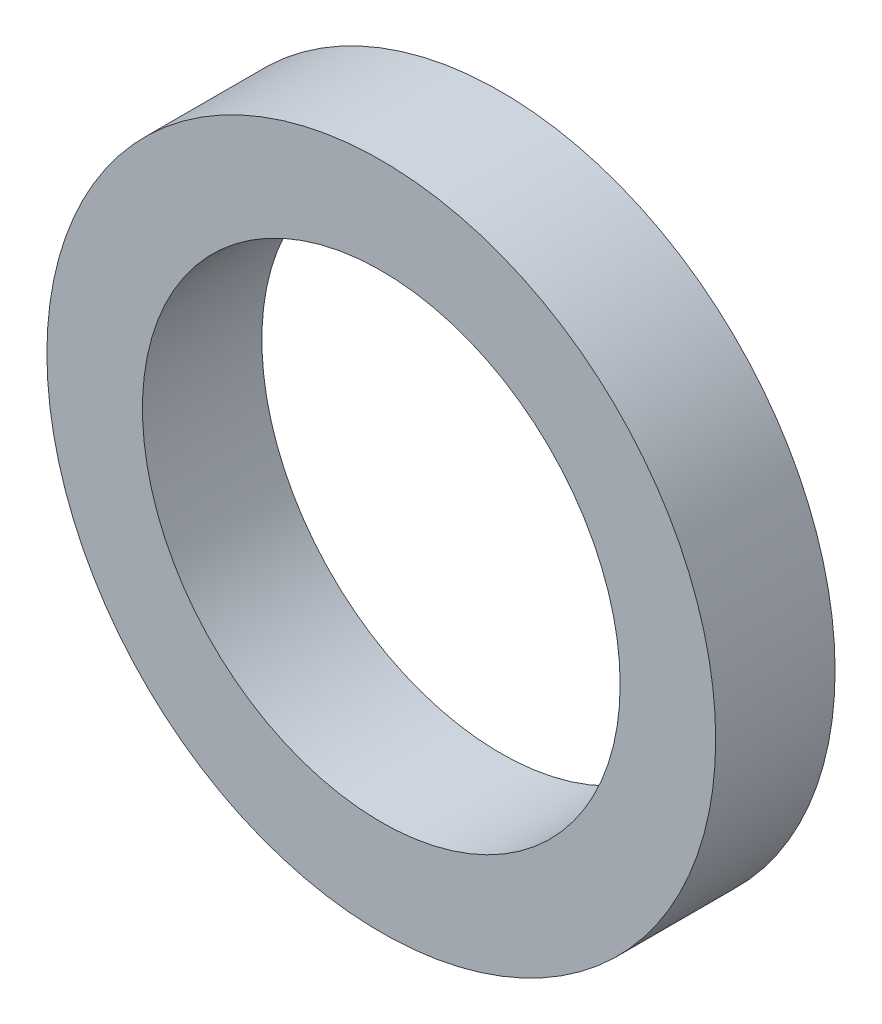
SolidWorks part; units mm, degrees
material "Chrome Stainless Steel"
ref_plane "Front Plane" through (0, 0, 0) normal (0, 0, 1) x (1, 0, 0)
ref_plane "Top Plane" through (0, 0, 0) normal (0, 1, 0) x (1, 0, 0)
ref_plane "Right Plane" through (0, 0, 0) normal (1, 0, 0) x (0, 0, -1)
sketch "Sketch1" plane through (0, 0, 0) normal (0, 0, 1) x (1, 0, 0)
  circle A0 centre (0, 0) radius 11.1125
  circle A1 centre (0, 0) radius 7.9375
  dimension "D1" = 22.225
  dimension "D2" = 15.875
extrude "Boss-Extrude1" add sketch "Sketch1" along normal blind 3.9675
